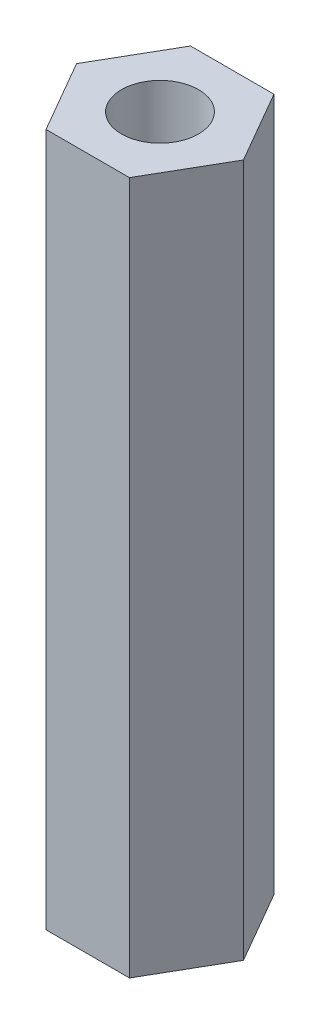
SolidWorks part; units mm, degrees
ref_plane "Front Plane" through (0, 0, 0) normal (0, 0, 1) x (1, 0, 0)
ref_plane "Top Plane" through (0, 0, 0) normal (0, 1, 0) x (1, 0, 0)
ref_plane "Right Plane" through (0, 0, 0) normal (1, 0, 0) x (0, 0, -1)
sketch "Sketch1" plane through (0, 0, 0) normal (0, 1, 0) x (1, 0, 0)
  line L1 (3.25, 0) -> (1.625, 2.8146)
  line L2 (1.625, 2.8146) -> (-1.625, 2.8146)
  line L3 (-1.625, 2.8146) -> (-3.25, 0)
  line L4 (-3.25, 0) -> (-1.625, -2.8146)
  line L5 (-1.625, -2.8146) -> (1.625, -2.8146)
  line L6 (1.625, -2.8146) -> (3.25, 0)
  circle A0 centre (0, 0) radius 2.8146 construction
  circle A1 centre (0, 0) radius 1.5
  dimension "D2" = 3
  dimension "D1" = 6.5
extrude "Boss-Extrude1" add sketch "Sketch1" along normal blind 27
